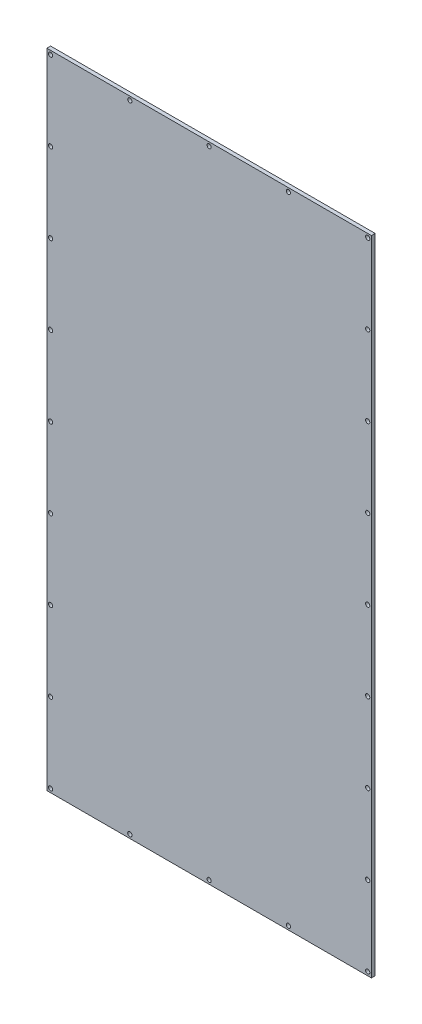
SolidWorks part; units mm, degrees
ref_plane "Front" through (0, 0, 0) normal (0, 0, 1) x (1, 0, 0)
ref_plane "Top" through (0, 0, 0) normal (0, 1, 0) x (1, 0, 0)
ref_plane "Right" through (0, 0, 0) normal (1, 0, 0) x (0, 0, -1)
sketch "Sketch1" plane through (0, 0, 0) normal (0, 0, 1) x (1, 0, 0)
  line L1 (0, 0) -> (260, 0)
  line L2 (0, 0) -> (0, 515)
  line L3 (0, 515) -> (260, 515)
  line L4 (260, 0) -> (260, 515)
  dimension "D1" = 515
  dimension "D2" = 260
extrude "Boss-Extrude1" add sketch "Sketch1" along normal blind 2.9972
hole_wizard "M3 Clearance Hole1" positions "Sketch3" profile "Sketch2" hole size "M3" standard "ANSI Metric" end condition through all
sketch "Sketch3" plane through (0, 0, 2.9972) normal (0, 0, 1) x (1, 0, 0)
  line L0 (257, 0) -> (257, 515) construction
  line L1 (0, 0) -> (260, 0) construction
  line L2 (260, 515) -> (0, 515) construction
  line L3 (257, 515) -> (260, 512) construction
  line L4 (260, 0) -> (260, 515) construction
  line L5 (260, 512) -> (0, 512) construction
  line L6 (0, 515) -> (0, 0) construction
  point P22 (257, 257.5)
  dimension "D1" = 3
  dimension "D2" = 3
sketch "Sketch2" plane through (257, 257.5, 2.9972) normal (1, 0, 0) x (0, -1, 0)
  line L0 (0, 0) -> (0, 2.9972)
  line L1 (0, 2.9972) -> (1.7, 2.9972)
  line L2 (1.7, 2.9972) -> (1.7, 0)
  line L5 (1.7, 0) -> (0, 0)
  line L11 (0, -6.35) -> (0, 107.95) construction
  dimension "Thru Hole Dia." = 3.4
  dimension "Thru Hole Depth" = 2.9972
hole_wizard "M3 Clearance Hole2" positions "Sketch4" profile "Sketch5" hole size "M3" standard "ANSI Metric" end condition through all
sketch "Sketch4" plane through (0, 0, 2.9972) normal (0, 0, 1) x (1, 0, 0)
  line L0 (257.0028, 515) -> (257.0028, 0) construction
  line L1 (260, 515) -> (0, 515) construction
  line L2 (0, 0) -> (260, 0) construction
  line L4 (260, 3) -> (0, 3) construction
  line L5 (260, 0) -> (260, 515) construction
  line L6 (0, 515) -> (0, 0) construction
  line L8 (3, 0) -> (3, 515) construction
  line L10 (260, 512) -> (0, 512) construction
  point P27 (130, 512)
  dimension "D1" = 2.9972
  dimension "D2" = 3
  dimension "D3" = 3
  dimension "D4" = 3
sketch "Sketch5" plane through (130, 512, 2.9972) normal (1, 0, 0) x (0, -1, 0)
  line L0 (0, 0) -> (0, 2.9972)
  line L1 (0, 2.9972) -> (1.7, 2.9972)
  line L2 (1.7, 2.9972) -> (1.7, 0)
  line L5 (1.7, 0) -> (0, 0)
  line L11 (0, -6.35) -> (0, 107.95) construction
  dimension "Thru Hole Dia." = 3.4
  dimension "Thru Hole Depth" = 2.9972
pattern_linear "LPattern1" count 5 spacing 63.625 along (0, -1, 0) count 5 spacing 63.625 along (0, 1, 0) skipping (0, 4), (4, 0) of "M3 Clearance Hole1"
pattern_linear "LPattern2" count 3 spacing 63.5 along (1, 0, 0) count 3 spacing 63.5 along (-1, 0, 0) of "M3 Clearance Hole2"
ref_plane "Plane1" through (130, 0, 0) normal (-1, 0, 0) x (0, 0, 1)
ref_plane "Plane2" through (0, 257.5, 0) normal (0, 1, 0) x (1, 0, 0)
mirror "Mirror1" about plane through (130, 0, 0) normal (-1, 0, 0) of "M3 Clearance Hole1", "LPattern1"
mirror "Mirror2" about plane through (0, 257.5, 0) normal (0, 1, 0) of "M3 Clearance Hole2", "LPattern2"
equation "\"ABS_thickness_1/16\" = 1.524\t"
equation "\"ABS_thickness_3/32\" = 2.3622"
equation "\"ABS_thickness_1/8\" = 2.9972\t"
equation "\"ABS_thickness_1/4\" = 5.9944"
equation "\"Bus_bar_thickness\" = 3.175"
equation "\"Connector_width\" = 20.2"
equation "\"Number_of_cells_long\" = 25"
equation "\"Number_of_cells_wide\" = 2"
equation "\"Cell_height\" = 65.0"
equation "\"Cell_diam\" = 18.0"
equation "\"Enclosure_Width\" = 292"
equation "\"Enclosure_Length\" = 260"
equation "\"Enclosure_Height\" = 515"
equation "\"D1@Sketch1\"=\"Enclosure_Height\""
equation "\"D2@Sketch1\"=\"Enclosure_Length\""
equation "\"D3@LPattern1\"=(\"Enclosure_Height\"-6)/8"
equation "\"D3@LPattern2\"=(\"Enclosure_Length\"-6)/4"
equation "\"D4@LPattern1\"=(\"Enclosure_Height\"-6)/8"
equation "\"D4@LPattern2\"=(\"Enclosure_Length\"-6)/4"
equation "\"D1@Boss-Extrude1\"=\"ABS_thickness_1/8\""
